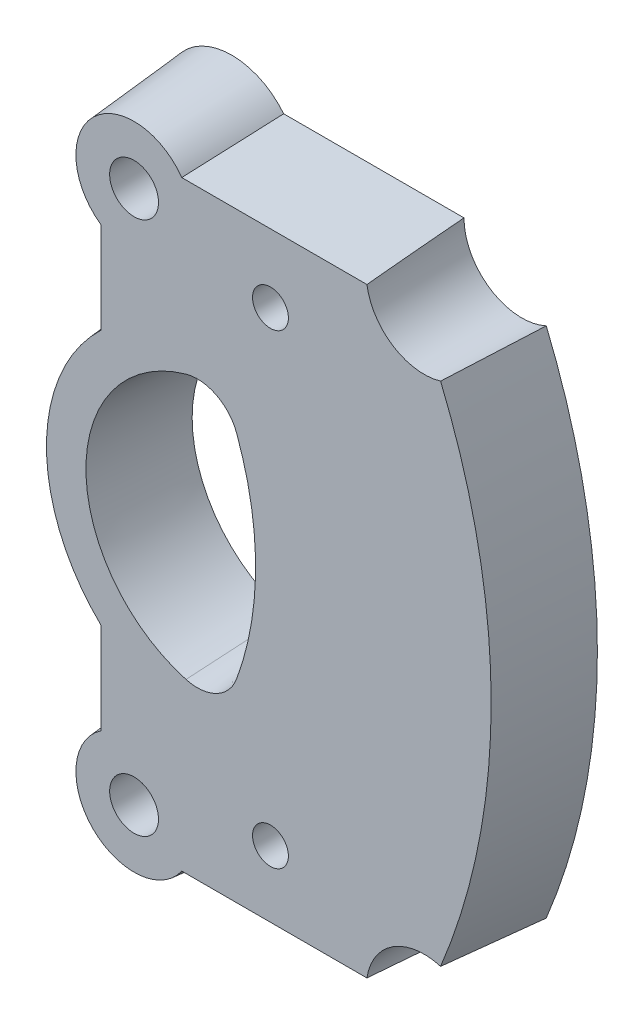
SolidWorks part; units mm, degrees
ref_plane "Front Plane" through (0, 0, 0) normal (0, 0, 1) x (1, 0, 0)
ref_plane "Top Plane" through (0, 0, 0) normal (0, 1, 0) x (1, 0, 0)
ref_plane "Right Plane" through (0, 0, 0) normal (1, 0, 0) x (0, 0, -1)
sketch "Sketch1" plane through (0, 0, 0) normal (0, 0, 1) x (1, 0, 0)
  line L0 (-195.012, 26.0629) -> (-195.012, 41.3471)
  line L1 (-134.5917, -54.0178) -> (-177.9369, -54.0178)
  line L3 (-134.5917, 58.4222) -> (-177.9369, 58.4222)
  line L4 (-195.012, -36.9427) -> (-195.012, -21.6585)
  arc A0 (-134.5917, -54.0178) -> (-134.5917, 58.4222) centre (-242.5688, 2.2022) ccw
  arc A1 (-195.012, 26.0629) -> (-195.012, -21.6585) centre (-171.1513, 2.2022) ccw
  arc A4 (-177.9369, 58.4222) -> (-195.012, 41.3471) centre (-187.392, 50.8022) ccw
  arc A5 (-195.012, -36.9427) -> (-177.9369, -54.0178) centre (-187.392, -46.3978) ccw
extrude "Extrude1" add sketch "Sketch1" along normal blind 17.78 draft 5
sketch "Sketch3" plane through (10.3787, 21.5071, 17.78) normal (0, 0, 1) x (1, 0, 0)
  circle A0 centre (-197.7707, 29.2951) radius 4.445
  circle A1 centre (-197.7707, -67.9049) radius 4.445
  dimension "D1" = 8.89
extrude "Cut-Extrude2" cut sketch "Sketch3" against normal through all
sketch "Sketch4" plane through (0, 0, 17.78) normal (0, 0, 1) x (1, 0, 0)
  arc A0 (-177.9365, 26.2673) -> (-177.9365, -21.8629) centre (-171.1513, 2.2022) ccw
  arc A1 (-168.7173, 21.5642) -> (-168.7173, -17.1598) centre (-221.3459, 2.2022) cw
  arc A2 (-168.7173, 21.5642) -> (-177.9365, 26.2673) centre (-175.8687, 18.9332) ccw
  arc A3 (-168.7173, -17.1598) -> (-177.9365, -21.8629) centre (-175.8687, -14.5289) cw
  point P7 (-171.1513, 27.2055)
  point P10 (-171.1513, -22.8012)
  dimension "D1" = 7.62
extrude "Cut-Extrude3" cut sketch "Sketch4" against normal through all draft 5
sketch "Sketch5" plane through (0, 0, 0) normal (0, 0, -1) x (-1, 0, 0)
  circle A0 centre (134.5917, 58.4222) radius 10.5226
  circle A1 centre (134.5917, -54.0178) radius 10.5226
extrude "Cut-Extrude4" cut sketch "Sketch5" against normal blind 26.162
sketch "Sketch6" plane through (0, 0, 17.78) normal (0, 0, 1) x (1, 0, 0)
  circle A0 centre (-162.5631, 44.4304) radius 3.2639
  circle A1 centre (-162.5631, -40.3949) radius 3.2639
  dimension "D1" = 6.5278
extrude "Cut-Extrude5" cut sketch "Sketch6" against normal blind 7.62
